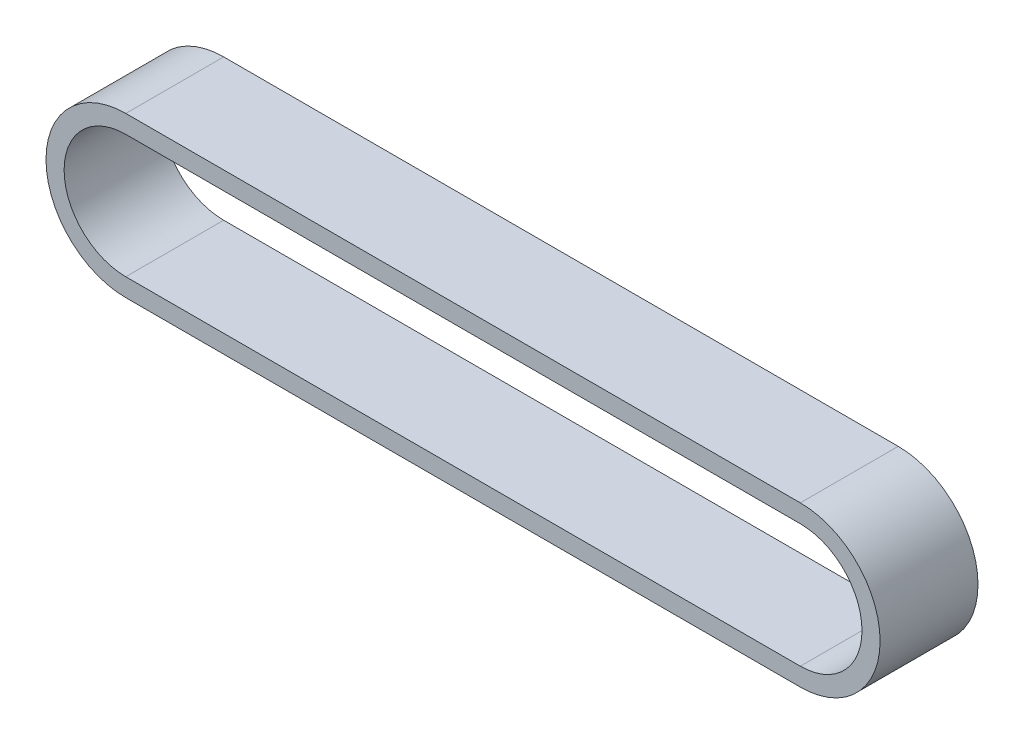
SolidWorks part; units mm, degrees
material "Silicon Rubber"
ref_plane "Front Plane" through (0, 0, 0) normal (0, 0, 1) x (1, 0, 0)
ref_plane "Top Plane" through (0, 0, 0) normal (0, 1, 0) x (1, 0, 0)
ref_plane "Right Plane" through (0, 0, 0) normal (1, 0, 0) x (0, 0, -1)
sketch "Sketch1" plane through (0, 0, 0) normal (0, 0, 1) x (1, 0, 0)
  line L0 (87.5, 0) -> (-87.5, 0) construction
  line L1 (87.5, -16) -> (-87.5, -16)
  line L2 (87.5, 16) -> (-87.5, 16)
  line L3 (87.5, -20.7) -> (-87.5, -20.7)
  line L4 (87.5, 20.7) -> (-87.5, 20.7)
  arc A0 (87.5, -16) -> (87.5, 16) centre (87.5, 0) ccw
  arc A1 (-87.5, 16) -> (-87.5, -16) centre (-87.5, 0) ccw
  arc A2 (-87.5, 20.7) -> (-87.5, -20.7) centre (-87.5, 0) ccw
  arc A3 (87.5, -20.7) -> (87.5, 20.7) centre (87.5, 0) ccw
  point P2 (0, 0)
  dimension "D1" = 16
  dimension "D2" = 175
  dimension "D3" = 4.7
extrude "Boss-Extrude1" add sketch "Sketch1" along normal blind 25.4
